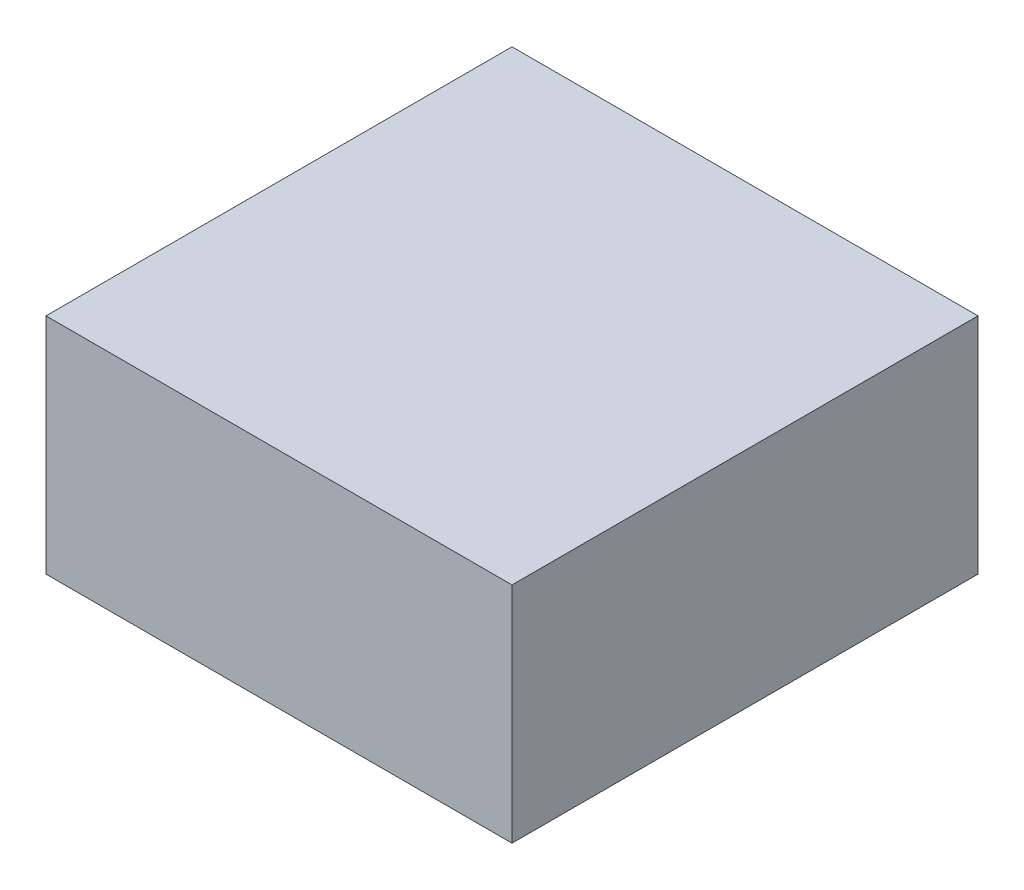
SolidWorks part; units mm, degrees
ref_plane "Front Plane" through (0, 0, 0) normal (0, 0, 1) x (1, 0, 0)
ref_plane "Top Plane" through (0, 0, 0) normal (0, 1, 0) x (1, 0, 0)
ref_plane "Right Plane" through (0, 0, 0) normal (1, 0, 0) x (0, 0, -1)
sketch "Sketch1" plane through (0, 0, 0) normal (0, 1, 0) x (1, 0, 0)
  line L1 (125, -125) -> (-125, -125)
  line L2 (125, -125) -> (125, 125)
  line L3 (125, 125) -> (-125, 125)
  line L4 (-125, -125) -> (-125, 125)
  line L5 (125, -125) -> (-125, 125) construction
  line L6 (125, 125) -> (-125, -125) construction
  point P0 (0, 0)
  dimension "D1" = 250
  dimension "D2" = 250
extrude "Boss-Extrude1" add sketch "Sketch1" along normal blind 120
sketch "Sketch2" [suppressed] plane through (0, 0, 0) normal (0, 1, 0) x (1, 0, 0)
  circle A0 centre (0, 0) radius 125
  dimension "D1" = 250
extrude "Boss-Extrude2" [suppressed] add sketch "Sketch2" along normal blind 120
